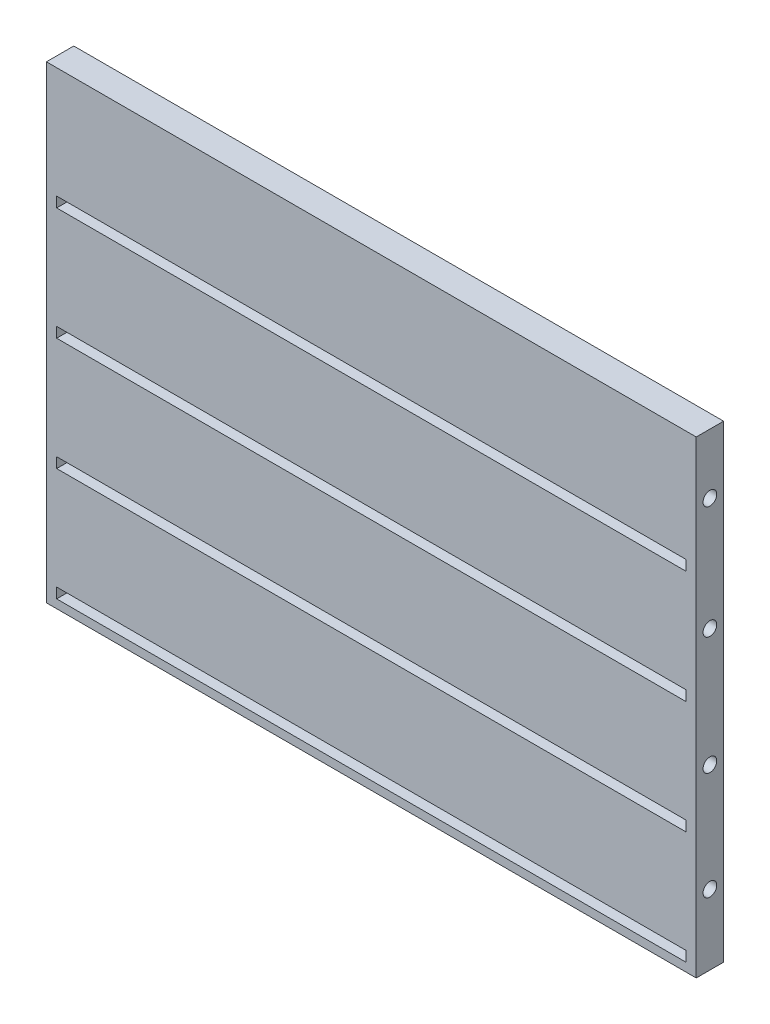
SolidWorks part; units mm, degrees
ref_plane "Front Plane" through (0, 0, 0) normal (0, 0, 1) x (1, 0, 0)
ref_plane "Top Plane" through (0, 0, 0) normal (0, 1, 0) x (1, 0, 0)
ref_plane "Right Plane" through (0, 0, 0) normal (1, 0, 0) x (0, 0, -1)
sketch "Sketch1" plane through (0, 0, 0) normal (0, 0, 1) x (1, 0, 0)
  line L1 (0, 0) -> (76, 0)
  line L2 (0, 0) -> (0, -54.8)
  line L3 (0, -54.8) -> (76, -54.8)
  line L4 (76, 0) -> (76, -54.8)
extrude "Boss-Extrude1" add sketch "Sketch1" along normal blind 3.2
sketch "Sketch2" plane through (0, 0, 0) normal (1, 0, 0) x (0, 0, -1)
  line L0 (-3.2, 0) -> (-3.2, -1) construction
  line L2 (-3.2, 0) -> (-3.2, -54.8) construction
  line L3 (-3.2, -1) -> (-3.2, -13) construction
  line L4 (-3.2, -14.2) -> (-3.2, -26.2) construction
  line L5 (-3.2, -13) -> (-2, -13)
  line L6 (-3.2, -13) -> (-3.2, -14.2)
  line L7 (-3.2, -14.2) -> (-2, -14.2)
  line L8 (-2, -13) -> (-2, -14.2)
  line L9 (-3.2, -27.4) -> (-3.2, -39.4) construction
  line L10 (-3.2, -26.2) -> (-2, -26.2)
  line L11 (-3.2, -26.2) -> (-3.2, -27.4)
  line L12 (-3.2, -27.4) -> (-2, -27.4)
  line L13 (-2, -26.2) -> (-2, -27.4)
  line L14 (-3.2, -40.6) -> (-3.2, -52.6) construction
  line L15 (-3.2, -39.4) -> (-2, -39.4)
  line L16 (-3.2, -39.4) -> (-3.2, -40.6)
  line L17 (-3.2, -40.6) -> (-2, -40.6)
  line L18 (-2, -39.4) -> (-2, -40.6)
  line L20 (-3.2, -52.6) -> (-2, -52.6)
  line L21 (-3.2, -52.6) -> (-3.2, -53.8)
  line L22 (-3.2, -53.8) -> (-2, -53.8)
  line L23 (-2, -52.6) -> (-2, -53.8)
extrude "Cut-Extrude1" cut sketch "Sketch2" along normal blind 73.6 from offset 1.2
sketch "Sketch3" plane through (0, 0, 0) normal (1, 0, 0) x (0, 0, -1)
  line L0 (-1.6, 0) -> (-1.6, -1) construction
  line L1 (-3.2, 0) -> (0, 0) construction
  line L2 (-1.6, -1) -> (-1.6, -13) construction
  line L3 (-1.6, -13) -> (-1.6, -14.2) construction
  line L4 (-1.6, -14.2) -> (-1.6, -26.2) construction
  line L5 (-1.6, -26.2) -> (-1.6, -27.4) construction
  line L6 (-1.6, -27.4) -> (-1.6, -39.4) construction
  line L7 (-1.6, -39.4) -> (-1.6, -40.6) construction
  line L8 (-1.6, -40.6) -> (-1.6, -52.6) construction
  line L9 (-1.6, -52.6) -> (-1.6, -53.8) construction
  line L10 (-1.6, -53.8) -> (-1.6, -54.8) construction
  line L11 (-3.2, -54.8) -> (0, -54.8) construction
  circle A0 centre (-1.6, -7) radius 0.8
  circle A1 centre (-1.6, -20.2) radius 0.8
  circle A2 centre (-1.6, -33.9989) radius 0.8
  circle A3 centre (-1.6, -46.6) radius 0.8
extrude "Cut-Extrude2" cut sketch "Sketch3" against normal blind 10 from offset 76
